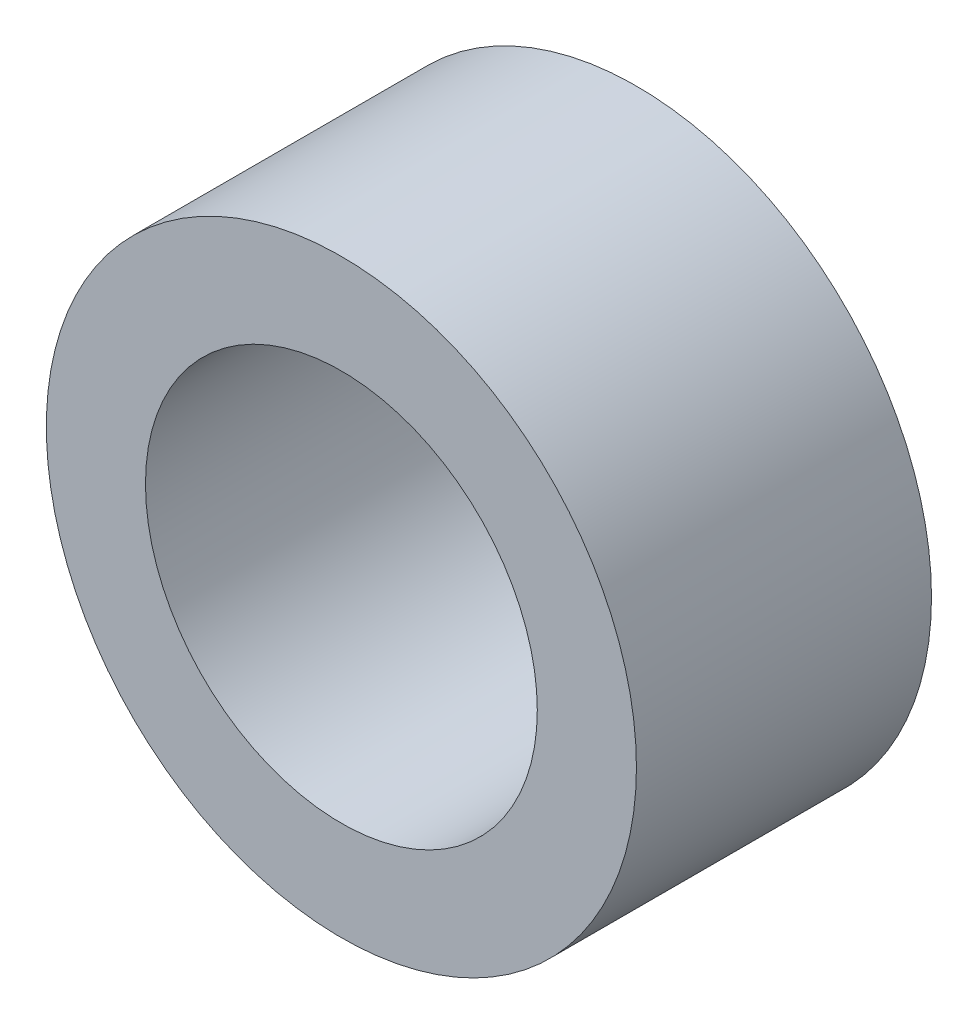
SolidWorks part; units mm, degrees
ref_plane "Front Plane" through (0, 0, 0) normal (0, 0, 1) x (1, 0, 0)
ref_plane "Top Plane" through (0, 0, 0) normal (0, 1, 0) x (1, 0, 0)
ref_plane "Right Plane" through (0, 0, 0) normal (1, 0, 0) x (0, 0, -1)
sketch "Sketch1" plane through (0, 0, 0) normal (0, 0, 1) x (1, 0, 0)
  circle A0 centre (0, 0) radius 3.175
  circle A1 centre (0, 0) radius 2.1082
  dimension "OD" = 6.35
  dimension "ID" = 4.2164
extrude "Extrude1" add sketch "Sketch1" along normal mid plane 3.175
sketch "Sketch2" plane through (0, 0, 0) normal (1, 0, 0) x (0, 0, -1)
  line L0 (-1.5875, -2.1082) -> (1.5875, -2.1082) construction
  line L3 (1.5875, 2.1082) -> (-1.5875, 2.1082) construction
  line L5 (-1.5875, -2.1082) -> (1.5875, -2.1082)
  line L6 (1.5875, 2.1082) -> (-1.5875, 2.1082)
sketch "Sketch4" plane through (0, 0, 1.5875) normal (0, 0, 1) x (1, 0, 0)
  line L0 (0, 0) -> (-1.4907, 1.4907)
  line L1 (0, -2.1828) -> (0, 2.1828) construction
  circle A0 centre (0, 0) radius 2.1082 construction
  dimension "D1" = 45
